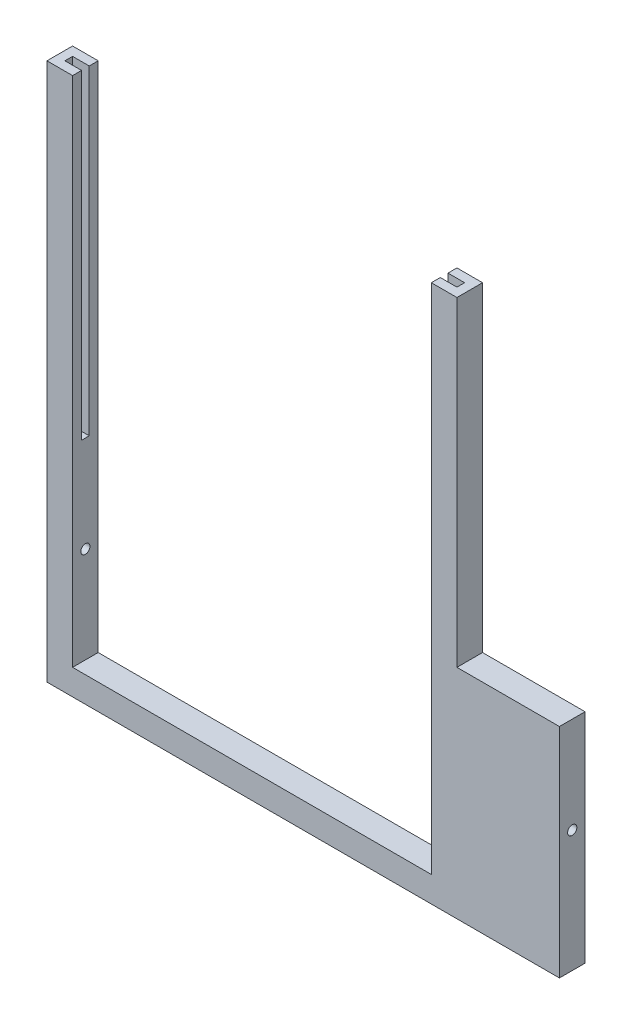
SolidWorks part; units mm, degrees
ref_plane "Front Plane" through (0, 0, 0) normal (0, 0, 1) x (1, 0, 0)
ref_plane "Top Plane" through (0, 0, 0) normal (0, 1, 0) x (1, 0, 0)
ref_plane "Right Plane" through (0, 0, 0) normal (1, 0, 0) x (0, 0, -1)
sketch "Sketch1" plane through (0, 0, 0) normal (0, 0, 1) x (1, 0, 0)
  line L0 (2, 17) -> (2, 2)
  line L1 (0, 0) -> (40, 0)
  line L2 (0, 0) -> (0, 17)
  line L3 (0, 17) -> (2, 17)
  line L4 (40, 0) -> (40, 17)
  line L5 (2, 2) -> (30, 2)
  line L6 (30, 2) -> (30, 17)
  line L7 (30, 17) -> (40, 17)
  dimension "D1" = 40
  dimension "D2" = 17
  dimension "D3" = 2
  dimension "D4" = 10
  dimension "D5" = 2
extrude "Boss-Extrude1" add sketch "Sketch1" along normal blind 2 contours L0 L5 L6 L7 L4 L1 L2 L3
sketch "Sketch2" plane through (40, 0, 0) normal (1, 0, 0) x (0, 0, -1)
  circle A0 centre (-1, 9.5) radius 0.36
  point P0 (-1, 9.5)
  dimension "D1" = 0.72
extrude "Cut-Extrude1" cut sketch "Sketch2" against normal through all both and the other way through all
sketch "Sketch3" plane through (0, 17, 0) normal (0, 1, 0) x (1, 0, 0)
  line L0 (0, -2) -> (2, -2)
  line L1 (2, -2) -> (2, -1.3)
  line L2 (2, -2) -> (2, 0) construction
  line L3 (2, -1.3) -> (0.7, -1.3)
  line L4 (0.7, -1.3) -> (0.7, -0.7)
  line L5 (0.7, -0.7) -> (2, -0.7)
  line L6 (2, -0.7) -> (2, 0)
  line L7 (2, 0) -> (0, 0)
  line L8 (0, 0) -> (0, -2)
  dimension "D1" = 0.7
  dimension "D2" = 0.7
  dimension "D3" = 1.3
extrude "Boss-Extrude2" add sketch "Sketch3" along normal blind 25 contours L4 L5 L6 L7 L8 L0 L1 L3
sketch "Sketch4" plane through (0, 17, 0) normal (0, 1, 0) x (1, 0, 0)
  line L0 (30, -2) -> (40, -2)
  line L1 (40, -2) -> (40, 0)
  line L2 (40, 0) -> (30, 0)
  line L3 (30, 0) -> (30, -0.7)
  line L4 (30, -2) -> (30, 0) construction
  line L5 (30, -0.7) -> (31.3, -0.7)
  line L6 (31.3, -0.7) -> (31.3, -1.3)
  line L7 (31.3, -1.3) -> (30, -1.3)
  line L8 (30, -1.3) -> (30, -2)
  dimension "D1" = 0.7
  dimension "D2" = 0.7
  dimension "D3" = 1.3
extrude "Boss-Extrude3" add sketch "Sketch4" along normal blind 25
sketch "Sketch5" plane through (0, 0, 2) normal (0, 0, 1) x (1, 0, 0)
  line L0 (40, 42) -> (32, 42)
  line L1 (30, 42) -> (40, 42) construction
  line L2 (32, 42) -> (32, 17)
  line L3 (32, 17) -> (40, 17)
  line L4 (40, 0) -> (40, 42) construction
  line L5 (40, 17) -> (40, 42)
  dimension "D1" = 8
  dimension "D2" = 25
extrude "Cut-Extrude2" cut sketch "Sketch5" against normal up to next
